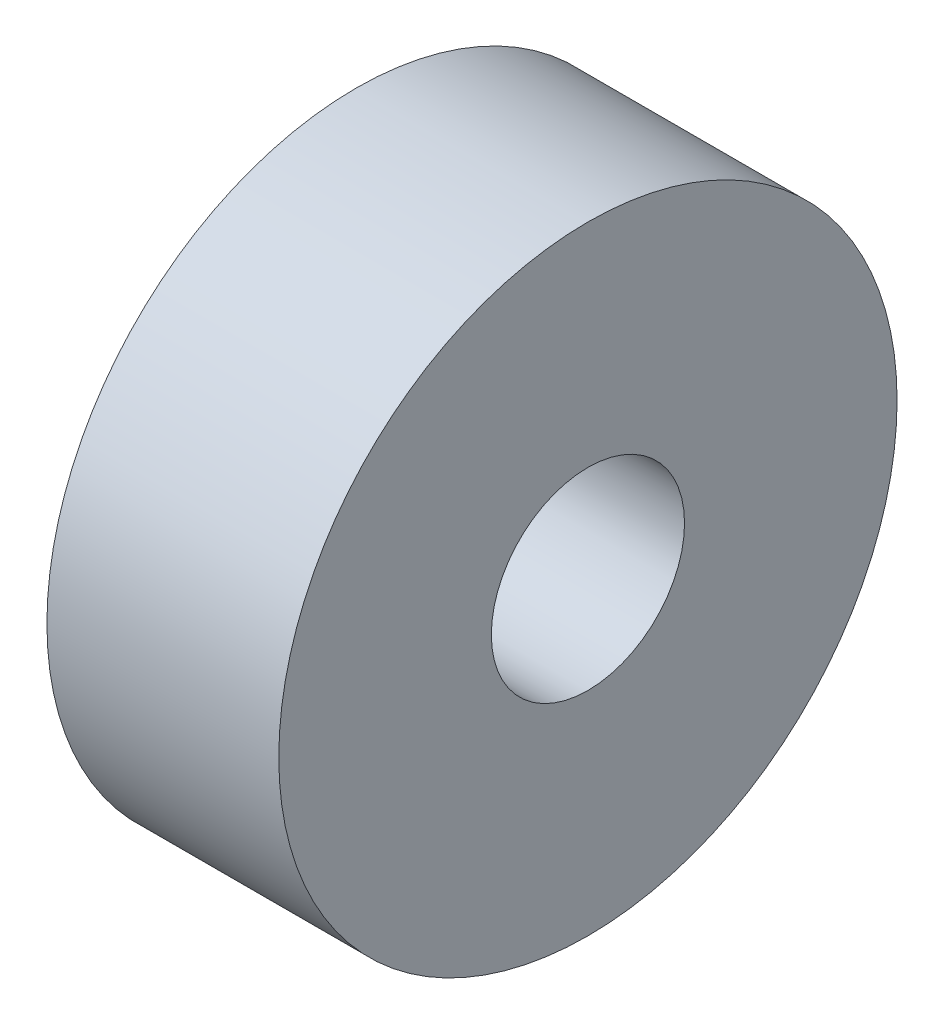
SolidWorks part; units mm, degrees
material "Stainless Steel (ferritic)"
ref_plane "Front Plane" through (0, 0, 0) normal (0, 0, 1) x (1, 0, 0)
ref_plane "Top Plane" through (0, 0, 0) normal (0, 1, 0) x (1, 0, 0)
ref_plane "Right Plane" through (0, 0, 0) normal (1, 0, 0) x (0, 0, -1)
sketch "Sketch1" plane through (0, 0, 0) normal (1, 0, 0) x (0, 0, -1)
  circle A0 centre (0, 0) radius 1.25
  circle A1 centre (0, 0) radius 4
  dimension "D1" = 2.5
  dimension "D2" = 8
extrude "Boss-Extrude1" add sketch "Sketch1" along normal blind 3
